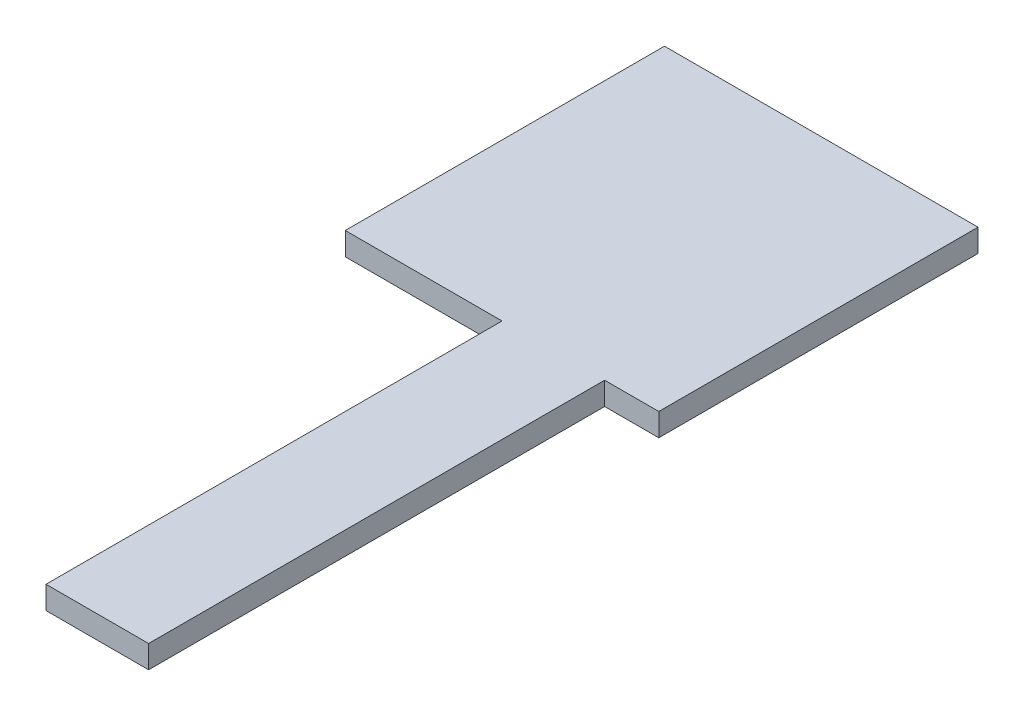
SolidWorks part; units mm, degrees
ref_plane "Front Plane" through (0, 0, 0) normal (0, 0, 1) x (1, 0, 0)
ref_plane "Top Plane" through (0, 0, 0) normal (0, 1, 0) x (1, 0, 0)
ref_plane "Right Plane" through (0, 0, 0) normal (1, 0, 0) x (0, 0, -1)
sketch "Sketch1" plane through (0, 0, 0) normal (0, 1, 0) x (1, 0, 0)
  line L1 (-13.75, -14) -> (13.75, -14)
  line L2 (-13.75, -14) -> (-13.75, 14)
  line L3 (-13.75, 14) -> (13.75, 14)
  line L4 (13.75, -14) -> (13.75, 14)
  line L5 (-13.75, -14) -> (13.75, 14) construction
  line L6 (-13.75, 14) -> (13.75, -14) construction
  point P0 (0, 0)
  dimension "D1" = 27.5
  dimension "D2" = 28
extrude "Boss-Extrude1" add sketch "Sketch1" along normal blind 2
sketch "Sketch2" plane through (0, 0, 14) normal (0, 0, 1) x (1, 0, 0)
  line L0 (-13.75, 2) -> (13.75, 2) construction
  line L1 (0, 0) -> (9, 0)
  line L2 (0, 0) -> (0, 2)
  line L3 (0, 2) -> (9, 2)
  line L4 (9, 0) -> (9, 2)
  dimension "D1" = 9
extrude "Boss-Extrude2" add sketch "Sketch2" along normal blind 40
